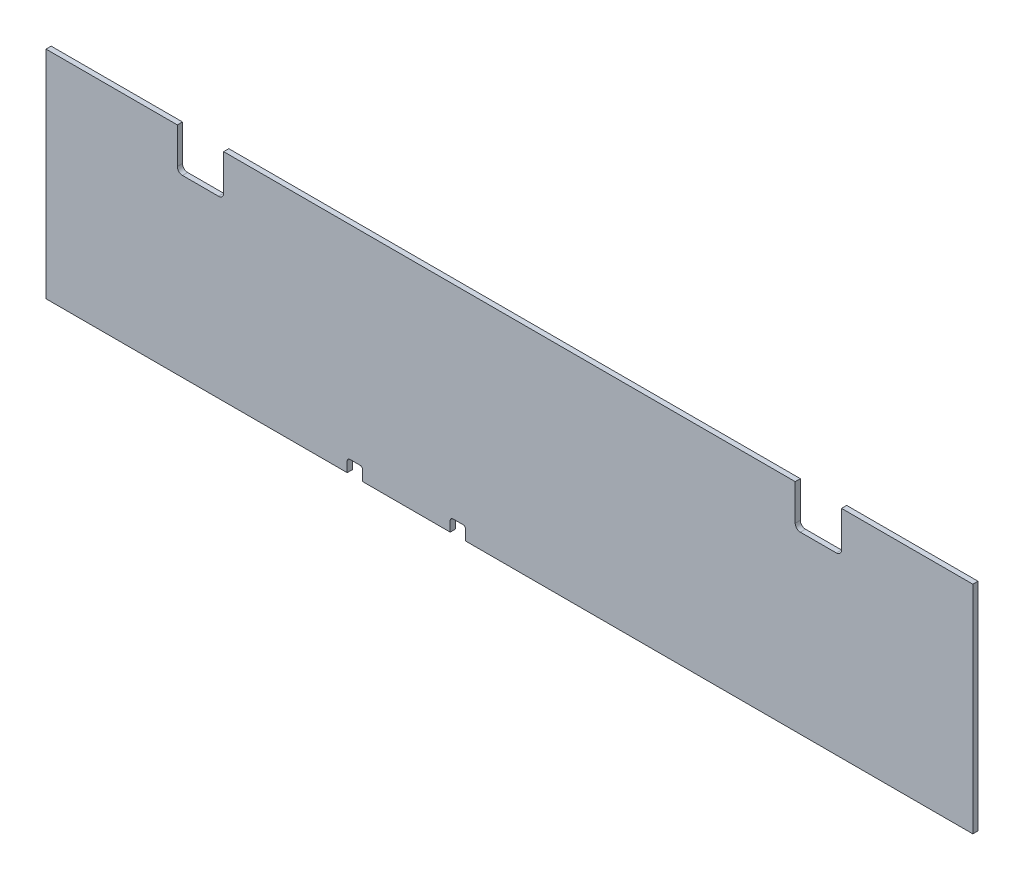
SolidWorks part; units mm, degrees
material "PC High Viscosity"
ref_plane "Front Plane" through (0, 0, 0) normal (0, 0, 1) x (1, 0, 0)
ref_plane "Top Plane" through (0, 0, 0) normal (0, 1, 0) x (1, 0, 0)
ref_plane "Right Plane" through (0, 0, 0) normal (1, 0, 0) x (0, 0, -1)
sketch "Sketch1" plane through (0, 0, 0) normal (0, 0, 1) x (1, 0, 0)
  line L0 (0, 0) -> (0, 266.7)
  line L1 (0, 266.7) -> (161.925, 266.7)
  line L2 (161.925, 266.7) -> (161.925, 215.9)
  line L3 (161.925, 215.9) -> (219.075, 215.9)
  line L4 (219.075, 215.9) -> (219.075, 266.7)
  line L5 (219.075, 266.7) -> (923.925, 266.7)
  line L6 (923.925, 266.7) -> (923.925, 215.9)
  line L7 (923.925, 215.9) -> (981.075, 215.9)
  line L8 (981.075, 215.9) -> (981.075, 266.7)
  line L9 (981.075, 266.7) -> (1143, 266.7)
  line L10 (1143, 266.7) -> (1143, 0)
  line L11 (1143, 0) -> (0, 0)
  dimension "D1" = 1143
  dimension "D2" = 57.15
  dimension "D3" = 704.85
  dimension "D4" = 266.7
  dimension "D5" = 50.8
extrude "Boss-Extrude1" add sketch "Sketch1" along normal blind 6.35
fillet "Fillet1" radius 6.35 4 edges at (923.925, 215.9, 3.175) (981.075, 215.9, 3.175) (219.075, 215.9, 3.175) (161.925, 215.9, 3.175)
sketch "Sketch2" plane through (0, 0, 6.35) normal (0, 0, 1) x (1, 0, 0)
  line L0 (371.475, 0) -> (390.525, 0)
  line L1 (371.475, 0) -> (371.475, 15.875)
  line L2 (390.525, 0) -> (390.525, 15.875)
  line L3 (371.475, 15.875) -> (390.525, 15.875)
  line L4 (0, 0) -> (1143, 0) construction
  line L5 (498.475, 0) -> (517.525, 0)
  line L6 (498.475, 0) -> (498.475, 15.875)
  line L7 (517.525, 0) -> (517.525, 15.875)
  line L8 (498.475, 15.875) -> (517.525, 15.875)
  point P4 (571.5, 0)
  point P7 (508, 15.875)
  point P8 (508, 0)
  point P11 (381, 0)
  dimension "D1" = 63.5
  dimension "D2" = 127
  dimension "D3" = 19.05
  dimension "D4" = 19.05
  dimension "D5" = 15.875
  dimension "D6" = 15.875
extrude "Cut-Extrude1" cut sketch "Sketch2" against normal through all
fillet "Fillet2" radius 3.175 4 edges at (498.475, 15.875, 3.175) (517.525, 15.875, 3.175) (390.525, 15.875, 3.175) (371.475, 15.875, 3.175)
